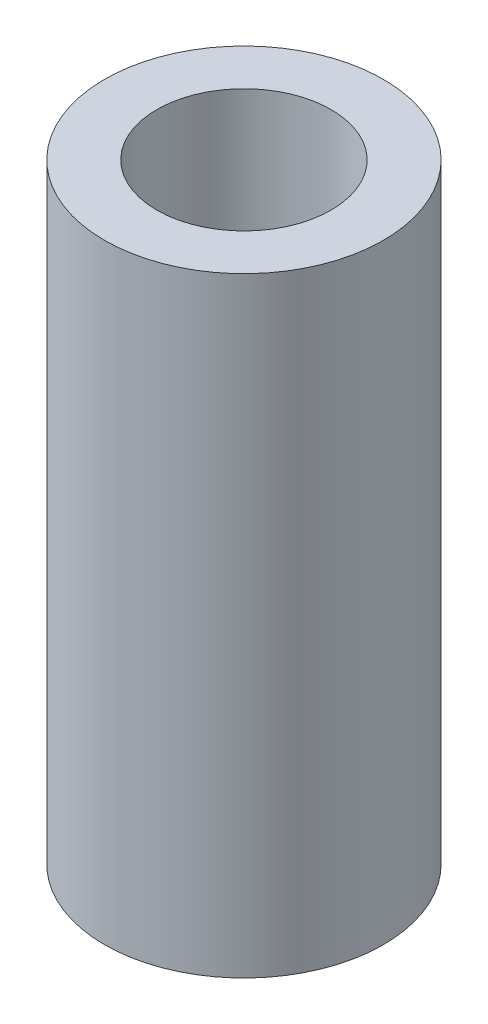
SolidWorks part; units mm, degrees
ref_plane "Front Plane" through (0, 0, 0) normal (0, 0, 1) x (1, 0, 0)
ref_plane "Top Plane" through (0, 0, 0) normal (0, 1, 0) x (1, 0, 0)
ref_plane "Right Plane" through (0, 0, 0) normal (1, 0, 0) x (0, 0, -1)
sketch "Sketch1" plane through (0, 0, 0) normal (0, 1, 0) x (1, 0, 0)
  circle A0 centre (0, 0) radius 5
  circle A1 centre (0, 0) radius 8
  dimension "D1" = 10
  dimension "D2" = 3
extrude "Boss-Extrude1" add sketch "Sketch1" along normal blind 35
